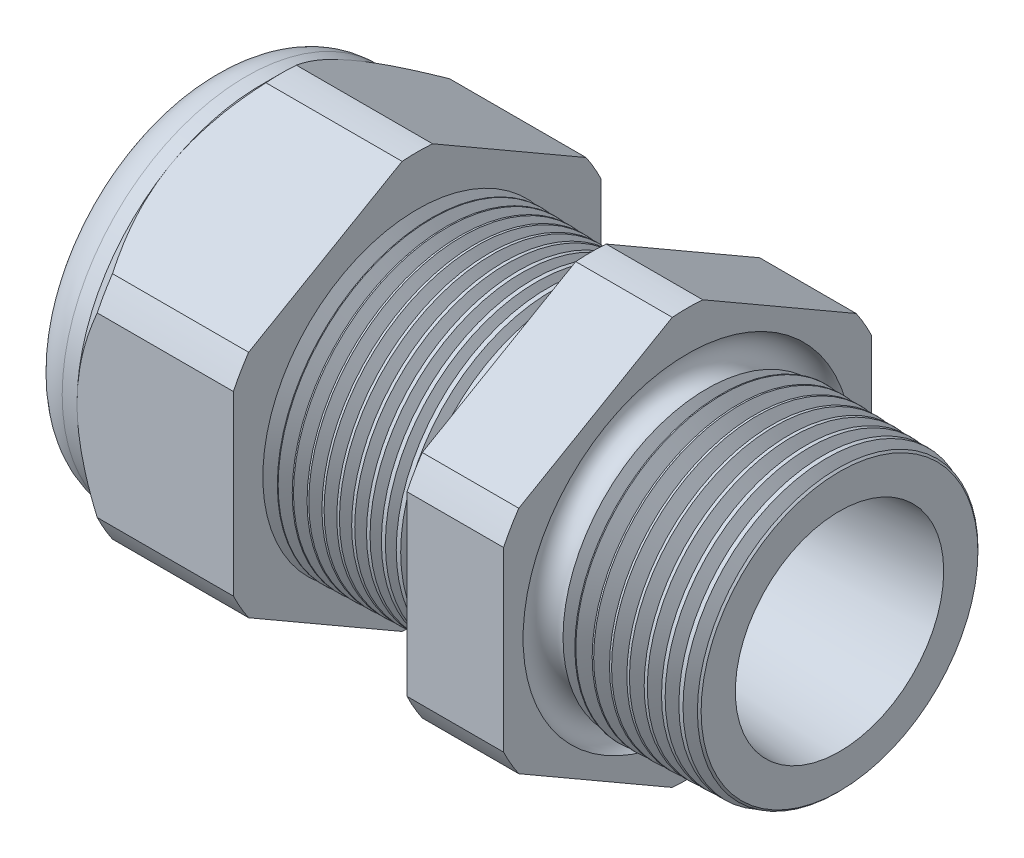
SolidWorks part; units mm, degrees
ref_plane "Front Plane" through (0, 0, 0) normal (0, 0, 1) x (1, 0, 0)
ref_plane "Top Plane" through (0, 0, 0) normal (0, 1, 0) x (1, 0, 0)
ref_plane "Right Plane" through (0, 0, 0) normal (1, 0, 0) x (0, 0, -1)
sketch "Sketch10" plane through (0, 0, 0) normal (0, 0, 1) x (1, 0, 0)
  line L0 (0, 0) -> (-115.3565, 0) construction
  line L1 (-32.766, 3.937) -> (-21.866, 3.937)
  line L2 (0, 5.3964) -> (0, 7.4284)
  line L3 (-7.874, 7.6346) -> (0, 7.4284)
  line L4 (-7.874, 19.05) -> (-7.874, 7.6346)
  line L5 (-7.874, 19.05) -> (-12.874, 19.05)
  line L6 (-12.874, 19.05) -> (-12.874, 7.7655)
  line L7 (-21.866, 8.001) -> (-12.874, 7.7655)
  line L8 (-21.866, 8.001) -> (-21.866, 19.05)
  line L9 (-21.866, 19.05) -> (-29.966, 19.05)
  line L10 (-29.966, 19.05) -> (-29.966, 9.525)
  line L11 (-29.966, 9.525) -> (-32.766, 9.525)
  line L12 (-32.766, 9.525) -> (-32.766, 3.937)
  line L13 (-21.866, 3.937) -> (0, 5.3964)
  dimension "D1" = 32.766
  dimension "D2" = 7.874
  dimension "D3" = 1.5
  dimension "D4" = 2.032
  dimension "A" = 16.002
  dimension "D6" = 19.05
  dimension "D8" = 38.1
  dimension "D9" = 2.8
  dimension "D10" = 8.1
  dimension "D11" = 5
  dimension "D" = 7.874
revolve "Revolve2" add sketch "Sketch10" angle 360 about L0
sketch "Sketch12" plane through (-29.966, 0, 0) normal (-1, 0, 0) x (0, 0, 1)
  line L1 (-0.7885, 10.5433) -> (-8.7365, 5.9545)
  line L2 (-9.525, 4.5888) -> (-9.525, -4.5888)
  line L3 (-8.7365, -5.9545) -> (-0.7885, -10.5433)
  line L4 (0.7885, -10.5433) -> (8.7365, -5.9545)
  line L5 (9.525, -4.5888) -> (9.525, 4.5888)
  line L6 (8.7365, 5.9545) -> (0.7885, 10.5433)
  circle A0 centre (0, 0) radius 9.525 construction
  arc A1 (0.7885, 10.5433) -> (-0.7885, 10.5433) centre (0, 0) ccw
  arc A2 (-8.7365, 5.9545) -> (-9.525, 4.5888) centre (0, 0) ccw
  arc A3 (-9.525, -4.5888) -> (-8.7365, -5.9545) centre (0, 0) ccw
  arc A4 (-0.7885, -10.5433) -> (0.7885, -10.5433) centre (0, 0) ccw
  arc A5 (8.7365, -5.9545) -> (9.525, -4.5888) centre (0, 0) ccw
  arc A6 (9.525, 4.5888) -> (8.7365, 5.9545) centre (0, 0) ccw
  dimension "D2" = 21.1455
  dimension "D1" = 19.05
extrude "Cut-Extrude2" cut sketch "Sketch12" against normal through all flip side to cut
fillet "Fillet4" radius 2.032 1 edges at (-32.766, 0, -9.525)
sketch "Sketch19" plane through (-29.966, 0, 0) normal (-1, 0, 0) x (0, 0, 1)
  line L0 (9.525, 0) -> (9.525, 4.5888) construction
  circle A0 centre (0, 0) radius 9.525
extrude "Cut-Extrude3" cut sketch "Sketch19" against normal blind 2 draft 45 flip side to cut
chamfer "Chamfer1" distance 0.254 angle 45 1 edges at (0, 0, -7.4284)
sketch "Sketch21" plane through (-32.766, 0, 0) normal (-1, 0, 0) x (0, 0, 1)
  circle A0 centre (0, 0) radius 3.937
  circle A2 centre (0, 0) radius 3.937 construction
extrude "plug" add sketch "Sketch21" against normal blind 3.81 separate body
sketch "Sketch22" plane through (-32.766, 0, 0) normal (-1, 0, 0) x (0, 0, 1)
  circle A0 centre (0, 0) radius 3.683
  circle A1 centre (0, 0) radius 3.937 construction
  dimension "D1" = 0.254
extrude "Cut-Extrude4" cut sketch "Sketch22" against normal blind 0.508
sketch "Sketch27" plane through (-32.258, 0, 0) normal (-1, 0, 0) x (0, 0, 1)
  line L0 (-4.3624, 0) -> (4.3624, 0) construction
  circle A0 centre (-2.1529, 0) radius 1.524
  circle A1 centre (0, 0) radius 3.683 construction
  dimension "D1" = 0.0061
  dimension "holedia" = 3.048
extrude "plugholes" cut sketch "Sketch27" against normal through all
pattern_circular "CirPattern1" count 2 over 360 about axis through (0, 0, 0) along (1, 0, 0) of "plugholes"
sketch "Sketch28" [suppressed] plane through (-29.464, 0, 0) normal (-1, 0, 0) x (0, 0, 1)
  circle A0 centre (0, 0) radius 0.762
  dimension "midholedia" = 3.048
extrude "midhole" [suppressed] cut sketch "Sketch28" against normal through all
sketch "Sketch29" plane through (0, 0, 0) normal (0, 0, 1) x (1, 0, 0)
  line L0 (-21.866, 8.001) -> (-21.133, 7.9818)
  line L1 (-12.874, 7.7655) -> (-21.866, 8.001) construction
  line L2 (-21.133, 7.9818) -> (-21.5161, 7.3566)
  line L3 (-21.5161, 7.3566) -> (-21.866, 8.001)
  dimension "D1" = 60
  dimension "D2" = 60
  dimension "D3" = 0.635
revolve "Cut-Revolve1" cut sketch "Sketch29" angle 360 about axis through (0, 0, 0) along (-1, 0, 0)
pattern_linear "LPattern1" count 12 spacing 0.762 along (1, 0, 0) of "Cut-Revolve1"
sketch "Sketch30" plane through (0, 0, 0) normal (0, 0, 1) x (1, 0, 0)
  line L0 (-7.874, 7.6346) -> (-6.9944, 7.6116)
  line L1 (-7.874, 10.5433) -> (-7.874, 5.9545) construction
  line L2 (-0.2539, 7.4351) -> (-7.874, 7.6346) construction
  line L3 (-6.9944, 7.6116) -> (-7.4542, 6.8614)
  line L4 (-7.4542, 6.8614) -> (-7.874, 7.6346)
  dimension "D1" = 60
  dimension "D2" = 60
  dimension "D3" = 0.762
revolve "Cut-Revolve2" cut sketch "Sketch30" angle 360 about axis through (0, 0, 0) along (-1, 0, 0)
pattern_linear "LPattern2" count 9 spacing 0.889 along (1, 0, 0) of "Cut-Revolve2"
sketch "Sketch31" [suppressed] plane through (-38.354, 0, 0) normal (-1, 0, 0) x (0, 0, 1)
  line L0 (-1.905, 1.905) -> (1.905, 1.905)
  line L1 (-1.905, -1.905) -> (1.905, -1.905)
  circle A0 centre (0, 0) radius 1.905 construction
  arc A1 (-1.905, 1.905) -> (-1.905, -1.905) centre (-1.905, 0) ccw
  arc A2 (1.905, 1.905) -> (1.905, -1.905) centre (1.905, 0) cw
extrude "Cut-Extrude5" [suppressed] cut sketch "Sketch31" against normal through all
sketch "Sketch32" plane through (0, 0, 0) normal (0, 0, 1) x (1, 0, 0)
  line L0 (-7.874, 10.5433) -> (-7.874, 5.9545) construction
  circle A0 centre (-7.747, 7.6346) radius 0.889
  dimension "D2" = 1.778
  dimension "D1" = 0.127
revolve "Cut-Revolve3" cut sketch "Sketch32" angle 360 about axis through (0, 0, 0) along (-1, 0, 0)
